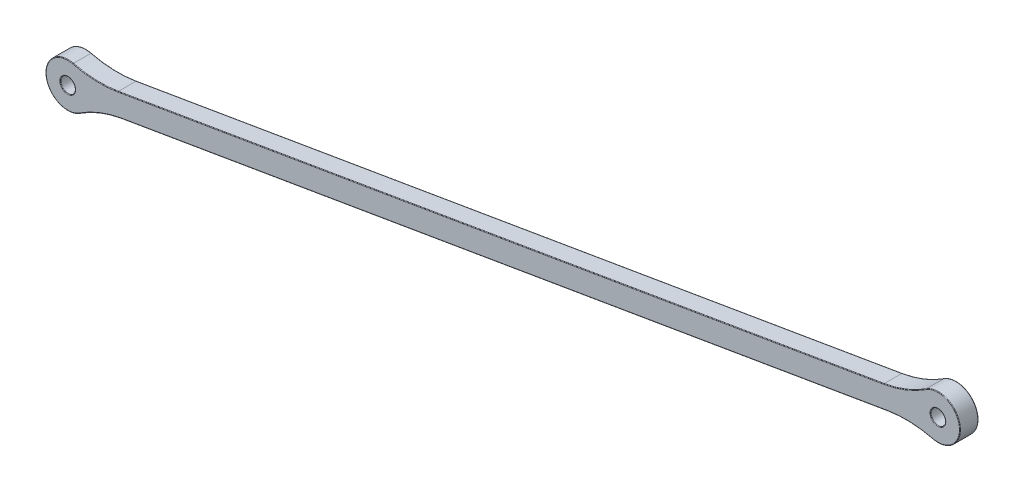
SolidWorks part; units mm, degrees
ref_plane "Front Plane" through (0, 0, 0) normal (0, 0, 1) x (1, 0, 0)
ref_plane "Top Plane" through (0, 0, 0) normal (0, 1, 0) x (1, 0, 0)
ref_plane "Right Plane" through (0, 0, 0) normal (1, 0, 0) x (0, 0, -1)
sketch "Sketch1" plane through (0, 0, 0) normal (0, 0, 1) x (1, 0, 0)
  line L0 (-71.3526, 303.2131) -> (-307.9763, 263.098) construction
  line L1 (-71.3526, 303.2131) -> (-307.9763, 263.098) construction
  line L2 (-307.9763, 263.098) -> (-71.3526, 303.2131) construction
  line L3 (-308.4777, 266.0558) -> (-71.854, 306.1709)
  line L4 (-307.4748, 260.1402) -> (-70.8511, 300.2553)
  arc A0 (-308.4777, 266.0558) -> (-307.4748, 260.1402) centre (-307.9763, 263.098) ccw
  arc A1 (-70.8511, 300.2553) -> (-71.854, 306.1709) centre (-71.3526, 303.2131) ccw
  circle A2 centre (-307.9763, 263.098) radius 6
  circle A3 centre (-71.3526, 303.2131) radius 6
  arc A4 (-308.4777, 266.0558) -> (-307.4748, 260.1402) centre (-307.9763, 263.098) cw
  arc A5 (-71.854, 306.1709) -> (-70.8511, 300.2553) centre (-71.3526, 303.2131) ccw
  circle A6 centre (-307.9763, 263.098) radius 2
  circle A7 centre (-71.3526, 303.2131) radius 2
  point P3 (-189.6644, 283.1555)
  dimension "D2" = 12
  dimension "D3" = 4
  dimension "D4" = 4
  dimension "D1" = 6
extrude "Boss-Extrude1" add sketch "Sketch1" against normal blind 5 contours L3 A2 L4 A0 | L3 A4 L4 A2 | L4 A3 L3 A1 | A5 L3 A3 L4 | A3 L3 A2 L4 | A4 A0 A6 | A1 A5 A7
fillet "Fillet1" radius 30 4 edges at (-302.3518, 261.0087, -2.5) (-75.9742, 299.3868, -2.5) (-76.9771, 305.3024, -2.5) (-303.3547, 266.9243, -2.5)
fillet "Fillet2" radius 0.15 20 edges at (-80.1071, 305.4124, -5) (-80.1071, 305.4124, 0) (-65.437, 304.216, 0) (-65.437, 304.216, -5) (-78.8931, 298.2513, -5) (-78.8931, 298.2513, 0) (-189.163, 280.1977, 0) (-189.163, 280.1977, -5) (-299.2217, 260.8987, -5) (-299.2217, 260.8987, 0) (-313.8919, 262.0951, -5) (-313.8919, 262.0951, 0) (-300.4358, 268.0598, -5) (-300.4358, 268.0598, 0) (-190.1659, 286.1133, 0) (-190.1659, 286.1133, -5) (-69.3526, 303.2131, -5) (-69.3526, 303.2131, 0) (-305.9763, 263.098, -5) (-305.9763, 263.098, 0)
